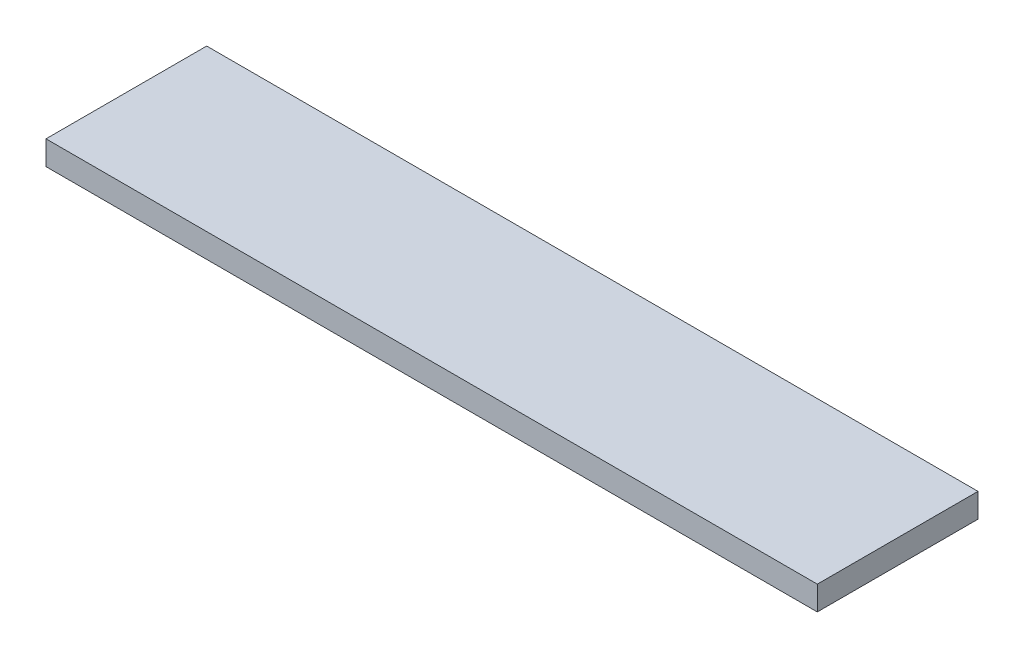
SolidWorks part; units mm, degrees
ref_plane "Ebene vorne" through (0, 0, 0) normal (0, 0, 1) x (1, 0, 0)
ref_plane "Ebene oben" through (0, 0, 0) normal (0, 1, 0) x (1, 0, 0)
ref_plane "Ebene rechts" through (0, 0, 0) normal (1, 0, 0) x (0, 0, -1)
sketch "Skizze1" plane through (0, 0, 0) normal (0, 1, 0) x (1, 0, 0)
  line L1 (0, 0) -> (192, 0)
  line L2 (0, 0) -> (0, 40)
  line L3 (0, 40) -> (192, 40)
  line L4 (192, 0) -> (192, 40)
  dimension "D1" = 192
  dimension "D2" = 40
extrude "Aufsatz-Linear austragen1" add sketch "Skizze1" along normal blind 6
